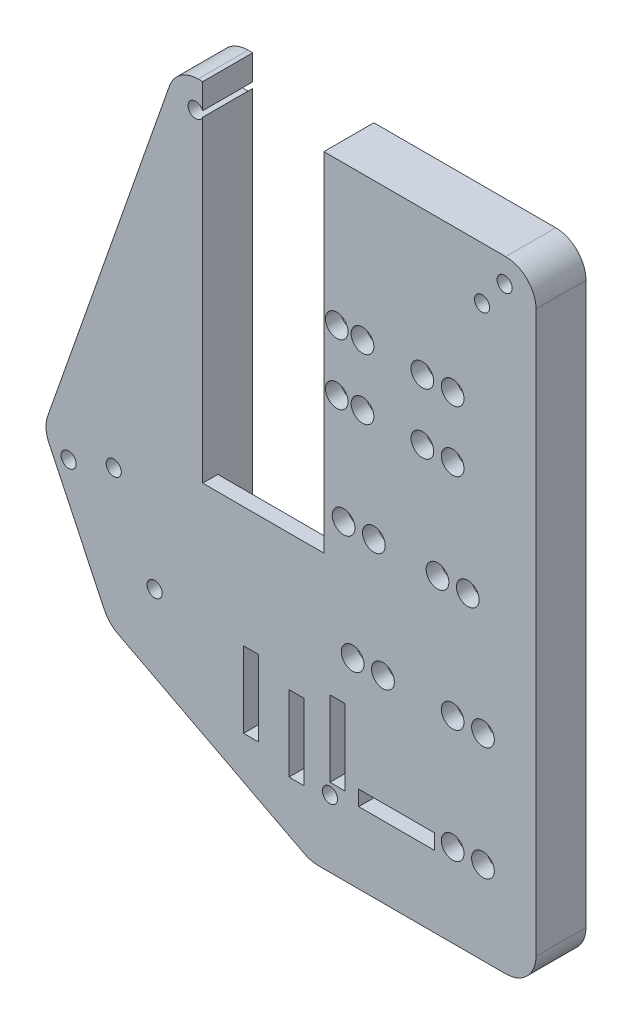
SolidWorks part; units mm, degrees
ref_plane "Front Plane" through (0, 0, 0) normal (0, 0, 1) x (1, 0, 0)
ref_plane "Top Plane" through (0, 0, 0) normal (0, 1, 0) x (1, 0, 0)
ref_plane "Right Plane" through (0, 0, 0) normal (1, 0, 0) x (0, 0, -1)
sketch "Sketch1" plane through (0, 0, 0) normal (0, 0, 1) x (1, 0, 0)
  line L6 (-20.066, -57.15) -> (46.99, -57.15) construction
  line L7 (-12.446, -73.152) -> (46.99, -73.152) construction
  line L8 (-3.3141, 6.35) -> (48.26, 6.35)
  line L9 (53.34, 1.27) -> (53.34, -92.71)
  line L10 (48.26, -97.79) -> (16.847, -97.79)
  line L16 (-8.1072, 2.9529) -> (-28.5162, -55.1739)
  line L18 (-20.066, -57.15) -> (-29.21, -57.15) construction
  line L26 (0, 0) -> (46.99, 0) construction
  line L27 (46.99, 0) -> (46.99, -88.9) construction
  line L28 (46.99, -88.9) -> (17.78, -88.9) construction
  line L29 (17.78, -88.9) -> (-12.446, -73.152) construction
  line L30 (-12.446, -73.152) -> (-20.066, -57.15) construction
  line L31 (-20.066, -57.15) -> (0, 0) construction
  line L32 (46.99, -57.15) -> (46.99, -88.9) construction
  line L33 (17.78, -88.9) -> (15.603, -97.79) construction
  line L34 (-12.446, -73.152) -> (-17.9301, -78.4424) construction
  line L35 (14.4997, -97.2152) -> (-16.7505, -80.9336)
  line L36 (-28.3096, -59.0409) -> (-18.9898, -78.6124)
  arc A0 (53.34, -92.71) -> (48.26, -97.79) centre (48.26, -92.71) cw
  arc A1 (14.4997, -97.2152) -> (16.847, -97.79) centre (16.847, -92.71) ccw
  arc A2 (-16.7505, -80.9336) -> (-18.9898, -78.6124) centre (-14.4033, -76.4284) cw
  arc A3 (-28.5162, -55.1739) -> (-28.3096, -59.0409) centre (-23.723, -56.8568) ccw
  arc A4 (-8.1072, 2.9529) -> (-3.3141, 6.35) centre (-3.3141, 1.27) cw
  arc A5 (48.26, 6.35) -> (53.34, 1.27) centre (48.26, 1.27) cw
  point P13 (53.34, -97.79)
  point P30 (53.34, 6.35)
  dimension "D8" = 5.08
  dimension "D1" = 88.9
  dimension "D2" = 29.21
  dimension "D3" = 59.436
  dimension "D4" = 67.056
  dimension "D5" = 104.14
  dimension "D6" = 82.55
  dimension "D7" = 46.99
  dimension "D9" = 61.6057
  dimension "D13" = 103.76
  dimension "D17" = 108.51
extrude "Boss-Extrude1" add sketch "Sketch1" along normal blind 2.54
sketch "Sketch3" plane through (0, 0, 0) normal (0, 0, 1) x (1, 0, 0)
  line L8 (0, 0) -> (46.99, 0) construction
  line L9 (46.99, 0) -> (46.99, -88.9) construction
  line L10 (46.99, -88.9) -> (17.78, -88.9) construction
  line L11 (17.78, -88.9) -> (-12.446, -73.152) construction
  line L12 (-12.446, -73.152) -> (-20.066, -57.15) construction
  line L13 (-20.066, -57.15) -> (0, 0) construction
sketch "Sketch4" plane through (0, 0, 0) normal (0, 0, -1) x (-1, 0, 0)
  line L0 (-46.99, 0) -> (-46.99, -88.9) construction
  line L1 (0, 0) -> (-46.99, 0) construction
  line L2 (-46.99, -88.9) -> (-17.78, -88.9) construction
  line L8 (-17.78, -1.143) -> (2.54, -1.143)
  line L9 (-17.78, -1.143) -> (-17.78, -51.943)
  line L10 (-17.78, -51.943) -> (2.54, -51.943)
  line L11 (2.54, -1.143) -> (2.54, -51.943)
  circle A0 centre (-39.37, -17.78) radius 1.905
  circle A1 centre (-34.29, -17.78) radius 1.905
  circle A2 centre (-39.37, -27.94) radius 1.905
  circle A3 centre (-34.29, -27.94) radius 1.905
  circle A4 centre (-41.91, -45.72) radius 1.905
  circle A5 centre (-36.83, -45.72) radius 1.905
  circle A6 centre (-44.45, -64.77) radius 1.905
  circle A7 centre (-39.37, -64.77) radius 1.905
  circle A8 centre (-44.45, -83.82) radius 1.905
  circle A9 centre (-39.37, -83.82) radius 1.905
  circle A10 centre (-24.257, -17.78) radius 1.905
  circle A11 centre (-19.939, -17.78) radius 1.905
  circle A12 centre (-24.257, -27.94) radius 1.905
  circle A13 centre (-19.939, -27.94) radius 1.905
  circle A14 centre (-26.162, -45.72) radius 1.905
  circle A15 centre (-21.082, -45.72) radius 1.905
  circle A16 centre (-27.686, -64.77) radius 1.905
  circle A17 centre (-22.606, -64.77) radius 1.905
  dimension "D6" = 3.81
  dimension "D7" = 17.78
  dimension "D11" = 3.81
  dimension "D12" = 3.81
  dimension "D16" = 3.81
  dimension "D17" = 3.81
  dimension "D21" = 3.81
  dimension "D22" = 3.81
  dimension "D30" = 3.81
  dimension "D31" = 3.81
  dimension "D35" = 3.81
  dimension "D36" = 3.81
  dimension "D40" = 3.81
  dimension "D41" = 3.81
  dimension "D45" = 3.81
  dimension "D46" = 3.81
  dimension "D3" = 5.08
  dimension "D5" = 7.62
  dimension "D8" = 5.08
  dimension "D9" = 27.94
  dimension "D10" = 17.78
  dimension "D13" = 5.08
  dimension "D14" = 27.94
  dimension "D15" = 17.78
  dimension "D18" = 5.08
  dimension "D19" = 22.733
  dimension "D20" = 17.78
  dimension "D23" = 5.08
  dimension "D24" = 27.94
  dimension "D25" = 27.051
  dimension "D26" = 50.8
  dimension "D27" = 20.32
  dimension "D28" = 27.94
  dimension "D29" = 45.72
  dimension "D32" = 4.318
  dimension "D33" = 10.16
  dimension "D34" = 5.08
  dimension "D37" = 4.318
  dimension "D38" = 45.72
  dimension "D39" = 45.72
  dimension "D42" = 5.08
  dimension "D43" = 20.828
  dimension "D44" = 2.54
  dimension "D47" = 5.08
  dimension "D48" = 24.13
  dimension "D49" = 2.54
  dimension "D50" = 5.08
  dimension "D51" = 5.08
  dimension "D52" = 24.13
  dimension "D53" = 24.13
  dimension "D54" = 19.304
  dimension "D55" = 24.13
  dimension "D57" = 1.143
  dimension "D58" = 29.21
extrude "Cut-Extrude2" cut sketch "Sketch4" against normal blind 25.4
sketch "Sketch5" plane through (0, 0, 2.54) normal (0, 0, 1) x (1, 0, 0)
  line L0 (-2.54, -1.143) -> (-2.54, 6.35)
  line L1 (48.26, 6.35) -> (-3.3141, 6.35) construction
  line L2 (17.78, -1.143) -> (17.78, 6.35)
  line L3 (17.78, 6.35) -> (-2.54, 6.35)
  line L4 (-2.54, -1.143) -> (17.78, -1.143)
extrude "Cut-Extrude3" cut sketch "Sketch5" against normal blind 5.08
sketch "Sketch6" plane through (0, 0, 2.54) normal (0, 0, 1) x (1, 0, 0)
  line L0 (0, 0) -> (46.99, 0) construction
  line L1 (46.99, 0) -> (46.99, -88.9) construction
  line L2 (17.78, -88.9) -> (17.78, -82.3142) construction
  line L3 (46.99, -88.9) -> (17.78, -88.9) construction
  line L4 (17.78, -88.9) -> (-12.446, -73.152) construction
  line L5 (-12.446, -73.152) -> (-20.066, -57.15) construction
  circle A0 centre (1.6002, -2.4384) radius 1.27
  circle A1 centre (44.2976, -2.4384) radius 1.27
  circle A2 centre (-17.4498, -57.15) radius 1.27
  circle A4 centre (-10.5918, -71.3486) radius 1.27
  circle A5 centre (18.796, -86.5378) radius 1.27
  dimension "D1" = 2.54
  dimension "D3" = 2.54
  dimension "D7" = 2.54
  dimension "D9" = 2.54
  dimension "D11" = 2.54
  dimension "D2" = 2.4384
  dimension "D4" = 2.4384
  dimension "D5" = 2.6924
  dimension "D6" = 45.3898
  dimension "D8" = 2.6162
  dimension "D10" = 2.5866
  dimension "D12" = 1.016
  dimension "D13" = 2.3622
  dimension "D14" = 2.4561
  dimension "D15" = 2.3621
sketch "Sketch8" plane through (0, 0, 2.54) normal (0, 0, 1) x (1, 0, 0)
  line L0 (46.99, 0) -> (46.99, -88.9) construction
  line L1 (23.622, -83.2866) -> (36.322, -83.2866)
  line L2 (23.622, -83.2866) -> (23.622, -85.8266)
  line L3 (23.622, -85.8266) -> (36.322, -85.8266)
  line L4 (36.322, -83.2866) -> (36.322, -85.8266)
  line L5 (0, 0) -> (46.99, 0) construction
  line L7 (18.796, -72.009) -> (21.336, -72.009)
  line L8 (18.796, -72.009) -> (18.796, -84.709)
  line L9 (18.796, -84.709) -> (21.336, -84.709)
  line L10 (21.336, -72.009) -> (21.336, -84.709)
  line L11 (11.938, -74.676) -> (14.478, -74.676)
  line L12 (11.938, -74.676) -> (11.938, -87.376)
  line L13 (11.938, -87.376) -> (14.478, -87.376)
  line L14 (14.478, -74.676) -> (14.478, -87.376)
  line L15 (4.318, -72.136) -> (6.858, -72.136)
  line L16 (4.318, -72.136) -> (4.318, -84.836)
  line L17 (4.318, -84.836) -> (6.858, -84.836)
  line L18 (6.858, -72.136) -> (6.858, -84.836)
  dimension "D1" = 12.7
  dimension "D2" = 2.54
  dimension "D3" = 10.668
  dimension "D4" = 83.2866
  dimension "D5" = 12.7
  dimension "D6" = 2.54
  dimension "D7" = 25.654
  dimension "D8" = 72.009
  dimension "D9" = 12.7
  dimension "D10" = 2.54
  dimension "D11" = 32.512
  dimension "D12" = 74.676
  dimension "D13" = 12.7
  dimension "D14" = 2.54
  dimension "D15" = 72.136
  dimension "D16" = 40.132
extrude "Cut-Extrude5" cut sketch "Sketch8" against normal blind 5.08
sketch "Sketch9" plane through (0, 0, 0) normal (0, 0, -1) x (-1, 0, 0)
  line L0 (-48.26, -97.79) -> (-48.26, 1.27)
  line L1 (-48.26, 1.27) -> (-17.78, 1.27)
  line L2 (-17.78, 1.27) -> (-17.78, 6.35)
  line L3 (-17.78, 6.35) -> (-48.26, 6.35)
  line L4 (-53.34, -92.71) -> (-53.34, 1.27) construction
  line L5 (-53.34, 1.27) -> (-53.34, -92.71)
  line L6 (-17.78, 6.35) -> (-17.78, -51.943) construction
  line L7 (-48.26, 6.35) -> (-17.78, 6.35) construction
  line L12 (2.54, -51.943) -> (2.54, 6.35) construction
  line L13 (2.54, -82.6092) -> (2.54, 6.35)
  line L14 (3.3141, 6.35) -> (2.54, 6.35)
  line L15 (8.1072, 2.9529) -> (28.5162, -55.1739)
  line L17 (28.3096, -59.0409) -> (18.9898, -78.6124)
  line L18 (16.7505, -80.9336) -> (-14.4997, -97.2152)
  line L19 (-16.847, -97.79) -> (-16.847, -92.71)
  line L20 (-16.847, -92.71) -> (2.54, -82.6092)
  arc A0 (-53.34, -92.71) -> (-48.26, -97.79) centre (-48.26, -92.71) ccw
  arc A1 (-16.847, -97.79) -> (-14.4997, -97.2152) centre (-16.847, -92.71) ccw
  arc A2 (16.7505, -80.9336) -> (18.9898, -78.6124) centre (14.4033, -76.4284) ccw
  arc A3 (28.3096, -59.0409) -> (28.5162, -55.1739) centre (23.723, -56.8568) ccw
  arc A4 (3.3141, 6.35) -> (8.1072, 2.9529) centre (3.3141, 1.27) cw
  arc A5 (-48.26, 6.35) -> (-53.34, 1.27) centre (-48.26, 1.27) ccw
  point P19 (2.54, -68.8193)
  point P37 (2.54, -83.5082)
  dimension "D3" = 5.08
  dimension "D4" = 5.08
  dimension "D1" = 5.08
  dimension "D2" = 5.08
extrude "Boss-Extrude2" add sketch "Sketch9" along normal blind 5.842
sketch "Sketch10" plane through (0, 0, 2.54) normal (0, 0, 1) x (1, 0, 0)
  line L0 (48.26, 6.35) -> (17.78, 6.35) construction
  line L1 (53.34, -92.71) -> (53.34, 1.27) construction
  line L2 (-2.54, 6.35) -> (-3.3141, 6.35) construction
  line L3 (-8.1072, 2.9529) -> (-28.5162, -55.1739) construction
  line L4 (-28.3096, -59.0409) -> (-18.9898, -78.6124) construction
  circle A0 centre (48.0822, 2.286) radius 1.27
  circle A1 centre (-3.7187, 1.651) radius 1.27
  circle A2 centre (-25.0123, -59.762) radius 1.27
  dimension "D1" = 2.54
  dimension "D2" = 4.064
  dimension "D3" = 5.2578
  dimension "D4" = 4.699
  dimension "D5" = 4.572
  dimension "D6" = 2.667
  dimension "D7" = 4.826
extrude "Cut-Extrude6" cut sketch "Sketch10" against normal through all both and the other way through all
extrude "Cut-Extrude7" cut sketch "Sketch6" against normal through all both and the other way through all
